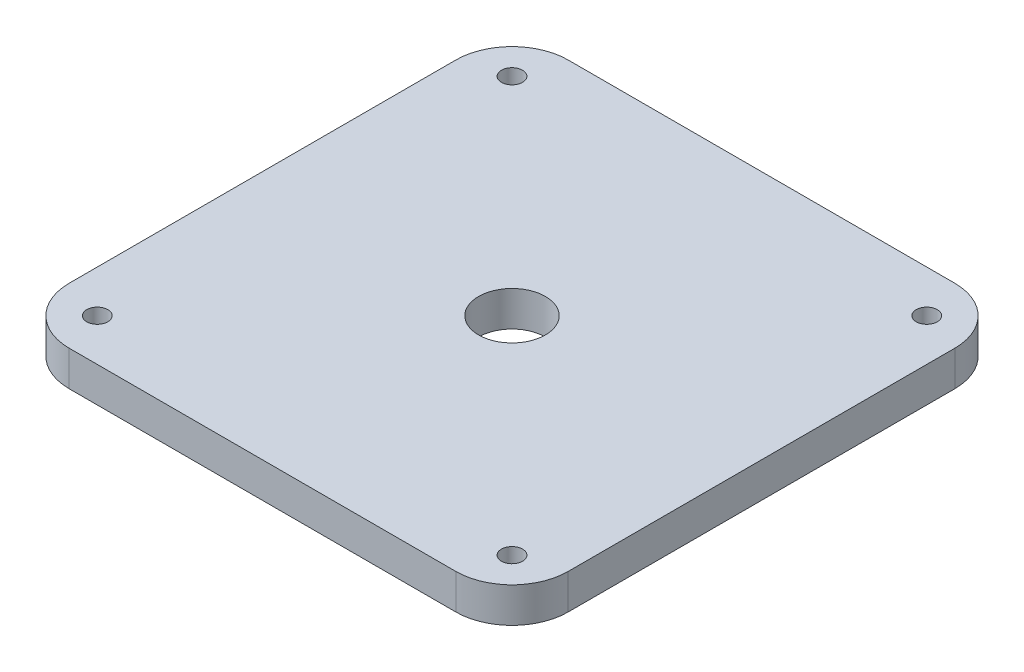
SolidWorks part; units mm, degrees
ref_plane "Front Plane" through (0, 0, 0) normal (0, 0, 1) x (1, 0, 0)
ref_plane "Top Plane" through (0, 0, 0) normal (0, 1, 0) x (1, 0, 0)
ref_plane "Right Plane" through (0, 0, 0) normal (1, 0, 0) x (0, 0, -1)
sketch "Sketch1" plane through (0, 0, 0) normal (0, 1, 0) x (1, 0, 0)
  line L1 (0, 0) -> (71, 0)
  line L2 (0, 0) -> (0, 71)
  line L3 (0, 71) -> (71, 71)
  line L4 (71, 0) -> (71, 71)
  circle A0 centre (6, 6) radius 1.5
  circle A1 centre (65, 6) radius 1.5
  circle A2 centre (65, 65) radius 1.5
  circle A3 centre (6, 65) radius 1.5
  circle A4 centre (35.5, 35.5) radius 4.75
  dimension "D3" = 3
  dimension "D4" = 3
  dimension "D5" = 3
  dimension "D6" = 3
  dimension "D15" = 9.5
  dimension "D1" = 71
  dimension "D2" = 71
  dimension "D7" = 6
  dimension "D8" = 6
  dimension "D9" = 6
  dimension "D10" = 6
  dimension "D11" = 6
  dimension "D12" = 6
  dimension "D13" = 6
  dimension "D14" = 6
extrude "Boss-Extrude1" add sketch "Sketch1" along normal blind 5
fillet "Fillet1" radius 8 4 edges at (0, 2.5, -71) (71, 2.5, -71) (0, 2.5, 0) (71, 2.5, 0)
